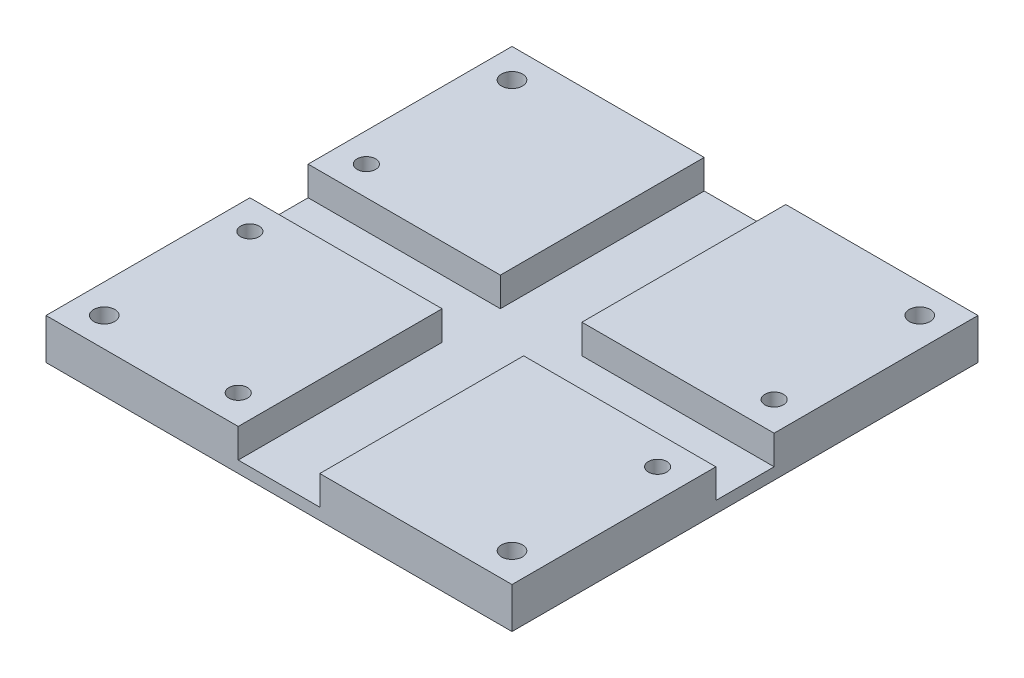
SolidWorks part; units mm, degrees
ref_plane "Front Plane" through (0, 0, 0) normal (0, 0, 1) x (1, 0, 0)
ref_plane "Top Plane" through (0, 0, 0) normal (0, 1, 0) x (1, 0, 0)
ref_plane "Right Plane" through (0, 0, 0) normal (1, 0, 0) x (0, 0, -1)
sketch "Sketch1" plane through (0, 0, 0) normal (0, 1, 0) x (1, 0, 0)
  line L1 (0, 0) -> (80, 0)
  line L2 (0, 0) -> (0, 80)
  line L3 (0, 80) -> (80, 80)
  line L4 (80, 0) -> (80, 80)
  dimension "D1" = 80
  dimension "D2" = 80
extrude "PCB" add sketch "Sketch1" along normal blind 2
sketch "Sketch7" plane through (0, 2, 0) normal (0, 1, 0) x (1, 0, 0)
  line L0 (0, 0) -> (80, 0) construction
  line L1 (80, 0) -> (47, 0)
  line L2 (80, 0) -> (80, 35)
  line L3 (80, 35) -> (47, 35)
  line L4 (47, 0) -> (47, 35)
  line L5 (80, 0) -> (80, 80) construction
  dimension "D1" = 35
  dimension "D2" = 33
  dimension "D3" = 0
  dimension "D4" = 0
extrude "LiPo Adafruit Chargers" add sketch "Sketch7" along normal blind 5
pattern_linear "LPattern2" count 2 spacing 47 along (-1, 0, 0) count 2 spacing 45 along (0, 0, -1) of "LiPo Adafruit Chargers"
sketch "Sketch4" plane through (0, 2, 0) normal (0, 1, 0) x (1, 0, 0)
  line L0 (0, 45) -> (0, 35) construction
  line L1 (47, 80) -> (33, 80) construction
  line L3 (80, 35) -> (80, 45) construction
  line L4 (33, 0) -> (47, 0) construction
  circle A0 centre (5, 75) radius 1.8
  circle A1 centre (75, 75) radius 1.8
  circle A2 centre (75, 5) radius 1.8
  circle A3 centre (5, 5) radius 1.8
  dimension "D3" = 3.6
  dimension "D4" = 5
  dimension "D6" = 3.6
  dimension "D9" = 3.6
  dimension "D12" = 3.6
  dimension "D1" = 5
  dimension "D2" = 5
  dimension "D5" = 5
  dimension "D7" = 5
  dimension "D8" = 5
  dimension "D10" = 5
  dimension "D11" = 5
extrude "Attachment holes" cut sketch "Sketch4" against normal through all both and the other way through all
sketch "Sketch8" plane through (0, 7, 0) normal (0, 1, 0) x (1, 0, 0)
  line L0 (0, 35) -> (0, 0) construction
  line L1 (33, 35) -> (0, 35) construction
  circle A0 centre (5, 30) radius 1.5875
  dimension "D1" = 3.175
  dimension "D2" = 5
  dimension "D3" = 5
extrude "Cut-Extrude1" cut sketch "Sketch8" against normal through all
pattern_linear "LPattern3" count 2 spacing 70 along (1, 0, 0) count 2 spacing 20 along (0, 0, -1) of "Cut-Extrude1"
sketch "Sketch9" plane through (0, 7, 0) normal (0, 1, 0) x (1, 0, 0)
  line L0 (33, 0) -> (33, 35) construction
  line L1 (0, 0) -> (33, 0) construction
  circle A0 centre (28, 5) radius 1.5875
  dimension "D1" = 3.175
  dimension "D2" = 5
  dimension "D3" = 5
extrude "Cut-Extrude2" cut sketch "Sketch9" against normal through all
